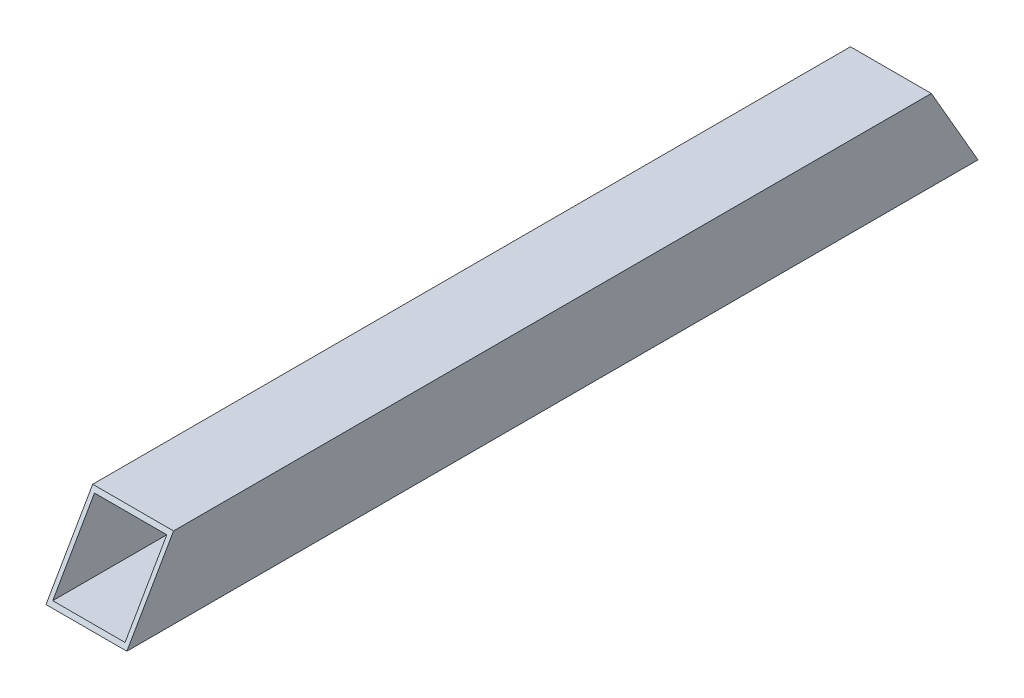
SolidWorks part; units mm, degrees
material "6061 Alloy"
ref_plane "Front Plane" through (0, 0, 0) normal (0, 0, 1) x (1, 0, 0)
ref_plane "Top Plane" through (0, 0, 0) normal (0, 1, 0) x (1, 0, 0)
ref_plane "Right Plane" through (0, 0, 0) normal (1, 0, 0) x (0, 0, -1)
sketch "Sketch1" plane through (0, 0, 0) normal (0, 0, 1) x (1, 0, 0)
  line L0 (-8.5, 8.5) -> (8.5, 8.5)
  line L1 (-9.5, -9.5) -> (9.5, -9.5)
  line L2 (-9.5, -9.5) -> (-9.5, 9.5)
  line L3 (-9.5, 9.5) -> (9.5, 9.5)
  line L4 (9.5, -9.5) -> (9.5, 9.5)
  line L5 (-9.5, -9.5) -> (9.5, 9.5) construction
  line L6 (-9.5, 9.5) -> (9.5, -9.5) construction
  line L7 (8.5, -8.5) -> (8.5, 8.5)
  line L8 (-8.5, -8.5) -> (8.5, -8.5)
  line L9 (-8.5, -8.5) -> (-8.5, 8.5)
  point P0 (0, 0)
  dimension "D1" = 19
  dimension "D2" = 19
  dimension "D3" = 1
extrude "Boss-Extrude1" add sketch "Sketch1" along normal blind 200
sketch "Sketch2" plane through (9.5, 0, 0) normal (1, 0, 0) x (0, 0, -1)
  line L0 (-200, -9.5) -> (-189.0303, 9.5)
  line L1 (-200, 9.5) -> (0, 9.5) construction
extrude "Cut-Extrude1" cut sketch "Sketch2" against normal through all and the other way through all
sketch "Sketch3" plane through (9.5, 0, 0) normal (1, 0, 0) x (0, 0, -1)
  line L0 (0, -9.5) -> (-10.9697, 9.5)
  line L1 (-189.0303, 9.5) -> (0, 9.5) construction
extrude "Cut-Extrude2" cut sketch "Sketch3" along normal through all and the other way through all flip side to cut
